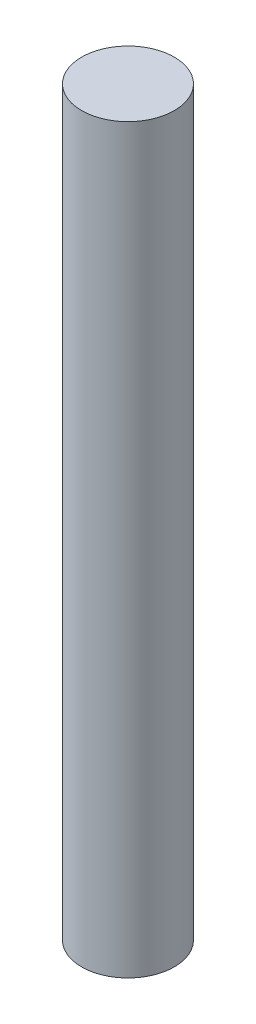
SolidWorks part; units mm, degrees
ref_plane "Front Plane" through (0, 0, 0) normal (0, 0, 1) x (1, 0, 0)
ref_plane "Top Plane" through (0, 0, 0) normal (0, 1, 0) x (1, 0, 0)
ref_plane "Right Plane" through (0, 0, 0) normal (1, 0, 0) x (0, 0, -1)
sketch "Sketch1" plane through (0, 0, 0) normal (0, 1, 0) x (1, 0, 0)
  circle A0 centre (0, 0) radius 3.175
  dimension "D1" = 6.35
extrude "Boss-Extrude1" add sketch "Sketch1" along normal blind 50.8 contours A0
equation "\"initial_height\"=2"
